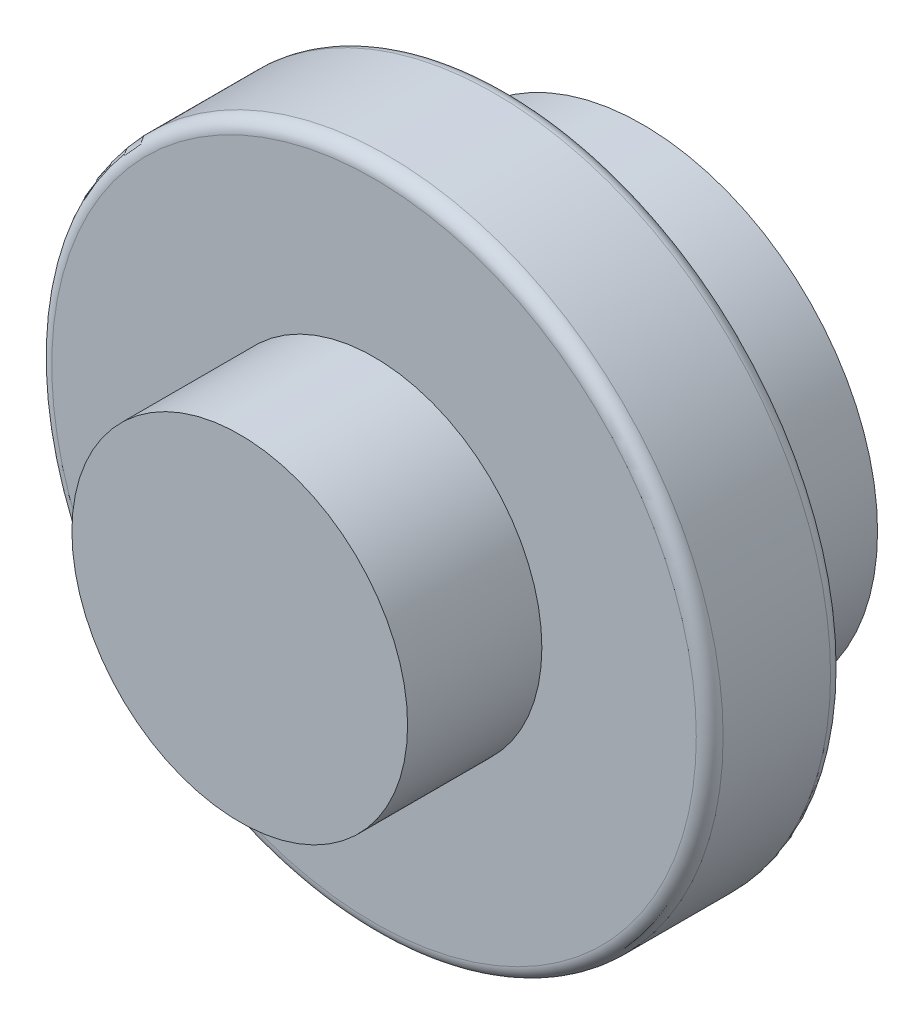
SolidWorks part; units mm, degrees
ref_plane "Front Plane" through (0, 0, 0) normal (0, 0, 1) x (1, 0, 0)
ref_plane "Top Plane" through (0, 0, 0) normal (0, 1, 0) x (1, 0, 0)
ref_plane "Right Plane" through (0, 0, 0) normal (1, 0, 0) x (0, 0, -1)
sketch "Sketch1" plane through (0, 0, 0) normal (0, 0, 1) x (1, 0, 0)
  circle A0 centre (0, 0) radius 17.5
  dimension "D1" = 35
extrude "Boss-Extrude1" add sketch "Sketch1" along normal blind 10
sketch "Sketch2" plane through (0, 0, 10) normal (0, 0, 1) x (1, 0, 0)
  circle A0 centre (0, 0) radius 25
  dimension "D1" = 50
extrude "Boss-Extrude2" add sketch "Sketch2" along normal blind 10
sketch "Sketch3" plane through (0, 0, 20) normal (0, 0, 1) x (1, 0, 0)
  circle A0 centre (0, 0) radius 12.5
  dimension "D1" = 25
extrude "Boss-Extrude3" add sketch "Sketch3" along normal blind 10
fillet "Fillet1" radius 1 2 edges at (25, 0, 10) (25, 0, 20)
